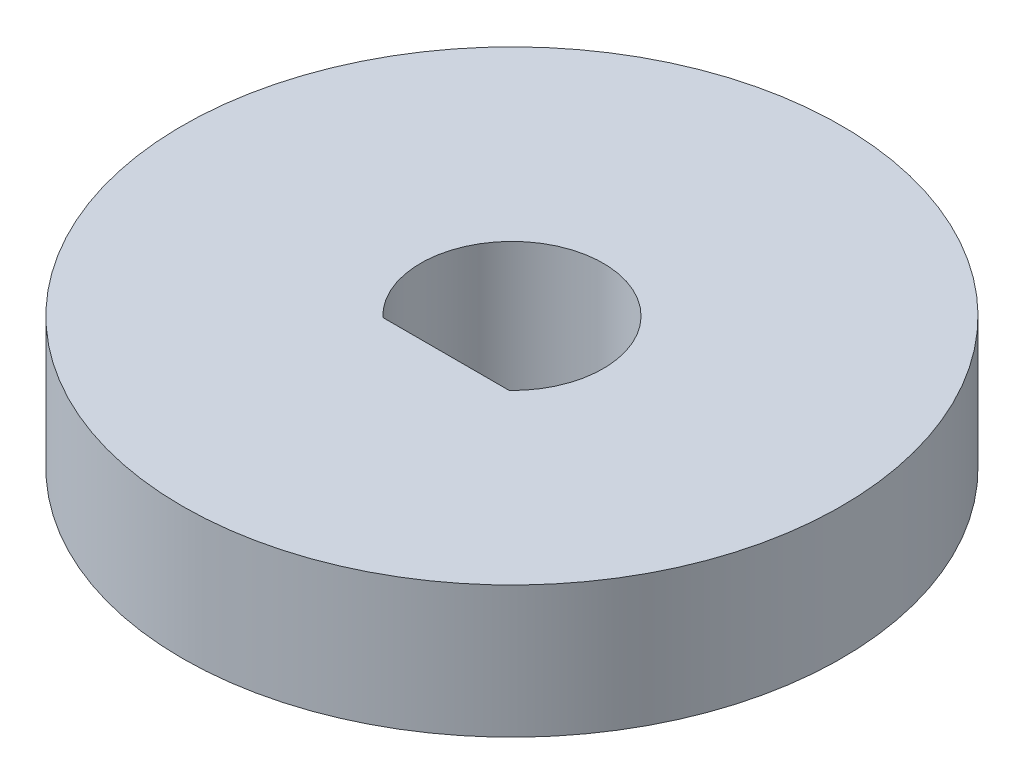
SolidWorks part; units mm, degrees
ref_plane "Front Plane" through (0, 0, 0) normal (0, 0, 1) x (1, 0, 0)
ref_plane "Top Plane" through (0, 0, 0) normal (0, 1, 0) x (1, 0, 0)
ref_plane "Right Plane" through (0, 0, 0) normal (1, 0, 0) x (0, 0, -1)
sketch "Sketch1" plane through (0, 0, 0) normal (0, 1, 0) x (1, 0, 0)
  line L0 (0, 2.7713) -> (0, -2)
  line L1 (-1.9183, -2) -> (1.9183, -2)
  arc A0 (1.9183, -2) -> (-1.9183, -2) centre (0, 0) ccw
  circle A1 centre (0, 0) radius 52.7713
  circle A2 centre (0, 0) radius 2.7713 construction
  circle A3 centre (0, 0) radius 10
  point P10 (0, -2)
  dimension "D1" = 50
  dimension "D2" = 2
extrude "Boss-Extrude1" add sketch "Sketch1" along normal blind 4 contours L1 A0 L0 | L0 A0 L1 | A3
